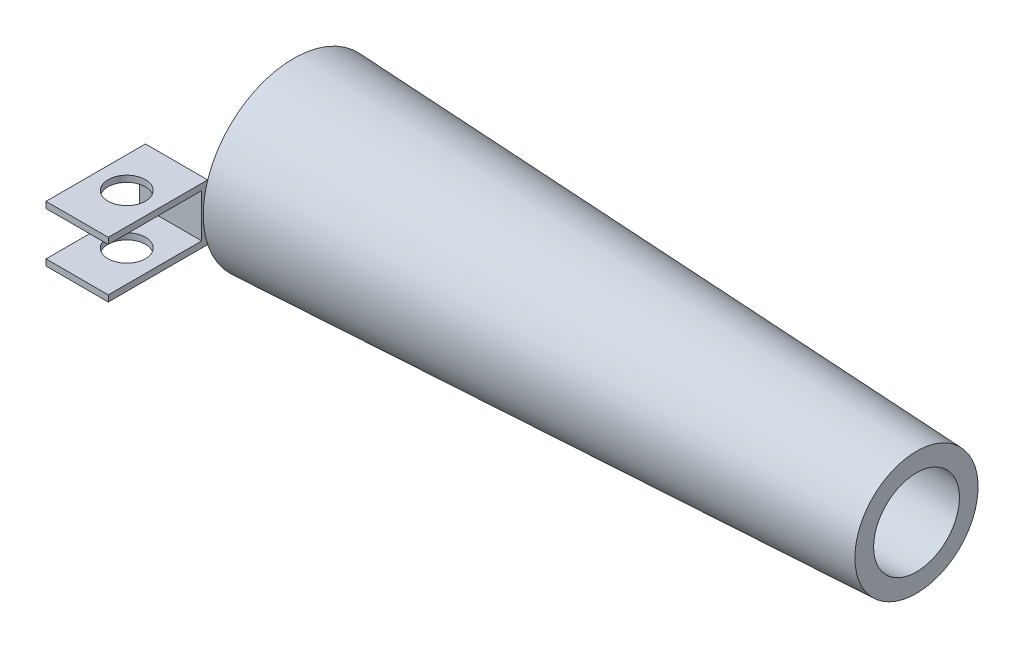
SolidWorks part; units mm, degrees
ref_plane "Front Plane" through (0, 0, 0) normal (0, 0, 1) x (1, 0, 0)
ref_plane "Top Plane" through (0, 0, 0) normal (0, 1, 0) x (1, 0, 0)
ref_plane "Right Plane" through (0, 0, 0) normal (1, 0, 0) x (0, 0, -1)
sketch "Sketch2" plane through (0, 0, 0) normal (0, 0, 1) x (1, 0, 0)
  line L1 (0, 0.3) -> (0, 1)
  line L2 (0, 1) -> (10, 0.5393)
  line L3 (10, 0.5393) -> (10, 0.239)
  line L4 (0.3, 0.3) -> (-0.0167, 0.3)
  line L5 (5.1433, 0.7568) -> (5.1329, 0.3) construction
  line L6 (0.3, 0.3) -> (0.3, 0.6859)
  line L7 (0.3, 0.6859) -> (10, 0.239)
  line L8 (0.3, 0.3) -> (5.1329, 0.3) construction
  line L9 (0, 0) -> (0, 1) construction
  line L10 (0, 1) -> (5.4262, 0.75) construction
  line L11 (5.4432, 0.75) -> (5.4262, 0) construction
  line L12 (0.3, 0.6859) -> (5.4124, 0.4503) construction
  line L13 (0, 0) -> (5.4262, 0) construction
  line L15 (0, -0.45) -> (5.3577, -0.45)
  dimension "D1" = 5.3577
  dimension "D2" = 10
revolve "Revolve2" add sketch "Sketch2" angle 360 about L15
sketch "Sketch3" plane through (0, 0, 0) normal (-1, 0, 0) x (0, 0, 1)
  line L0 (0.0166, 0.986) -> (0, -0.45) construction
  line L1 (-0.0092, -0.45) -> (2.9908, -0.45) construction
  line L2 (1.3784, 0) -> (2.9746, 0)
  line L3 (2.9746, 0) -> (2.9746, -0.9)
  line L5 (1.3784, -0.9) -> (2.9746, -0.9)
  circle A0 centre (0, -0.45) radius 1.45
  circle M5 centre (0, -0.45) radius 1.45
extrude "Boss-Extrude1" add sketch "Sketch3" along normal blind 1 separate body contours L5 L3 L2 M5
sketch "Sketch5" plane through (0, 0, 0) normal (0, 1, 0) x (1, 0, 0)
  line L1 (-1, -2.9746) -> (0, -2.9746) construction
  circle A0 centre (-0.5036, -2.1746) radius 0.3
  dimension "D1" = 0.8
extrude "Cut-Extrude2" cut sketch "Sketch5" against normal blind 1
sketch "Sketch6" plane through (0, 0, 2.9746) normal (0, 0, 1) x (1, 0, 0)
  line L0 (-1, 0) -> (-1, -0.9) construction
  line L1 (-1, -0.1) -> (0, -0.1)
  line L2 (-1, -0.1) -> (-1, -0.8)
  line L3 (-1, -0.8) -> (0, -0.8)
  line L4 (0, -0.1) -> (0, -0.8)
  line L5 (-1, 0) -> (0, 0) construction
  line L6 (-1, -0.9) -> (0, -0.9) construction
  line L7 (0, 0) -> (0, -0.9) construction
  dimension "D1" = 0.1
  dimension "D2" = 0.1
  dimension "D3" = 0
extrude "Cut-Extrude3" cut sketch "Sketch6" against normal blind 1.5
